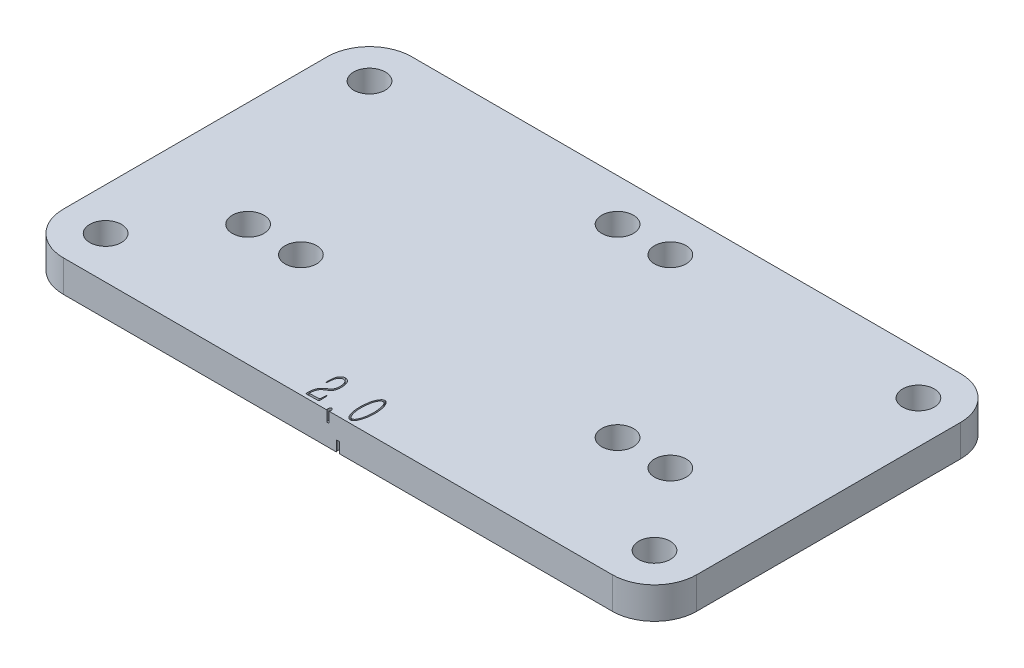
SolidWorks part; units mm, degrees
ref_plane "前视基准面" through (0, 0, 0) normal (0, 0, 1) x (1, 0, 0)
ref_plane "上视基准面" through (0, 0, 0) normal (0, 1, 0) x (1, 0, 0)
ref_plane "右视基准面" through (0, 0, 0) normal (1, 0, 0) x (0, 0, -1)
sketch "草图4" plane through (0, 0, 0) normal (0, 1, 0) x (1, 0, 0)
  line L0 (-1042.0123, 24.4569) -> (48957.9877, 24.4569) construction
  line L1 (-42.0123, 40.9569) -> (17.9877, 40.9569)
  line L2 (-42.0123, 40.9569) -> (-42.0123, 7.9569)
  line L3 (-42.0123, 7.9569) -> (17.9877, 7.9569)
  line L4 (17.9877, 40.9569) -> (17.9877, 7.9569)
  line L5 (-12.0123, -959.0431) -> (-12.0123, 49040.9569) construction
  point P7 (-42.0123, 24.4569)
  point P10 (-12.0123, 40.9569)
  dimension "D1" = 60
  dimension "D2" = 33
extrude "凸台-拉伸2" add sketch "草图4" against normal blind 3 contours L2 L1 L4 L3
sketch "草图7" plane through (0, 0, 0) normal (0, 1, 0) x (1, 0, 0)
  line L0 (-12.0123, 7.9569) -> (-9.5123, 7.9569)
  line L1 (-42.0123, 7.9569) -> (17.9877, 7.9569) construction
  line L2 (-9.5123, 7.9569) -> (-9.5123, 17.9569)
  line L3 (-9.5123, 17.9569) -> (-9.5123, 35.4569)
  line L4 (-9.5123, 17.9569) -> (7.9877, 17.9569)
  circle A0 centre (-9.5123, 35.4569) radius 1.5
  circle A1 centre (7.9877, 17.9569) radius 1.5
  circle A2 centre (-27.0123, 17.9569) radius 1.5
  circle A3 centre (-14.5123, 35.4569) radius 1.5
  circle A4 centre (2.9877, 17.9569) radius 1.5
  circle A5 centre (-32.0123, 17.9569) radius 1.5
  circle A6 centre (-14.5123, 35.9569) radius 1.5
  circle A7 centre (2.9877, 18.4569) radius 1.5
  circle A8 centre (-32.0123, 18.4569) radius 1.5
  circle A9 centre (-14.5123, 36.4569) radius 1.5
  circle A10 centre (2.9877, 18.9569) radius 1.5
  circle A11 centre (-32.0123, 18.9569) radius 1.5
  circle A12 centre (-14.5123, 36.9569) radius 1.5
  circle A13 centre (2.9877, 19.4569) radius 1.5
  circle A14 centre (-32.0123, 19.4569) radius 1.5
  circle A15 centre (-9.5123, 35.9569) radius 1.5
  circle A16 centre (7.9877, 18.4569) radius 1.5
  circle A17 centre (-27.0123, 18.4569) radius 1.5
  circle A18 centre (-9.5123, 36.4569) radius 1.5
  circle A19 centre (7.9877, 18.9569) radius 1.5
  circle A20 centre (-27.0123, 18.9569) radius 1.5
  circle A21 centre (-9.5123, 36.9569) radius 1.5
  circle A22 centre (7.9877, 19.4569) radius 1.5
  circle A23 centre (-27.0123, 19.4569) radius 1.5
  dimension "D5" = 3
  dimension "D6" = 3
  dimension "D1" = 2.5
  dimension "D2" = 10
  dimension "D3" = 17.5
  dimension "D4" = 17.5
  dimension "D7" = 2
  dimension "D8" = 4
sketch "草图8" plane through (0, 0, 0) normal (0, 1, 0) x (1, 0, 0)
  line L0 (-1042.0123, 24.4569) -> (48957.9877, 24.4569) construction
  line L1 (-42.0123, 40.9569) -> (-42.0123, 7.9569) construction
  line L2 (-12.0123, -958.5431) -> (-12.0123, 49041.4569) construction
  line L3 (-42.0123, 40.9569) -> (17.9877, 40.9569) construction
  line L4 (-42.0123, 40.9569) -> (-38.0123, 40.9569)
  line L5 (-42.0123, 40.9569) -> (17.9877, 40.9569) construction
  line L6 (-38.0123, 40.9569) -> (-38.0123, 36.9569)
  circle A0 centre (-38.0123, 36.9569) radius 1.5
  circle A1 centre (13.9877, 36.9569) radius 1.5
  circle A2 centre (13.9877, 11.9569) radius 1.5
  circle A3 centre (-38.0123, 11.9569) radius 1.5
  point P5 (-42.0123, 24.4569)
  point P10 (-12.0123, 40.9569)
  dimension "D1" = 3
  dimension "D2" = 4
  dimension "D3" = 4
extrude "切除-拉伸6" cut sketch "草图8" against normal blind 4
fillet "圆角2" radius 4 4 edges at (-42.0123, -1.5, -7.9569) (17.9877, -1.5, -7.9569) (17.9877, -1.5, -40.9569) (-42.0123, -1.5, -40.9569)
sketch "草图9" plane through (0, 0, 0) normal (0, 1, 0) x (1, 0, 0)
  line L0 (-12.0123, 40.9569) -> (-12.0123, 7.9569)
  line L1 (-38.0123, 40.9569) -> (13.9877, 40.9569) construction
  line L2 (-38.0123, 7.9569) -> (13.9877, 7.9569) construction
  circle A0 centre (-12.0123, 24.4569) radius 1.5
  dimension "D1" = 3
extrude "切除-拉伸7" cut sketch "草图7" against normal through all contours A12 | A14 | A13 | A23 | A22 | A21
sketch "草图10" plane through (0, 0, 0) normal (0, 1, 0) x (1, 0, 0)
  text T0 "2.0 "
extrude "切除-拉伸8" cut sketch "草图10" against normal blind 1
sketch "草图12" plane through (0, -3, 0) normal (0, -1, 0) x (1, 0, 0)
  text T0 "<b>2.0</b>"
extrude "切除-拉伸9" cut sketch "草图12" against normal blind 1
